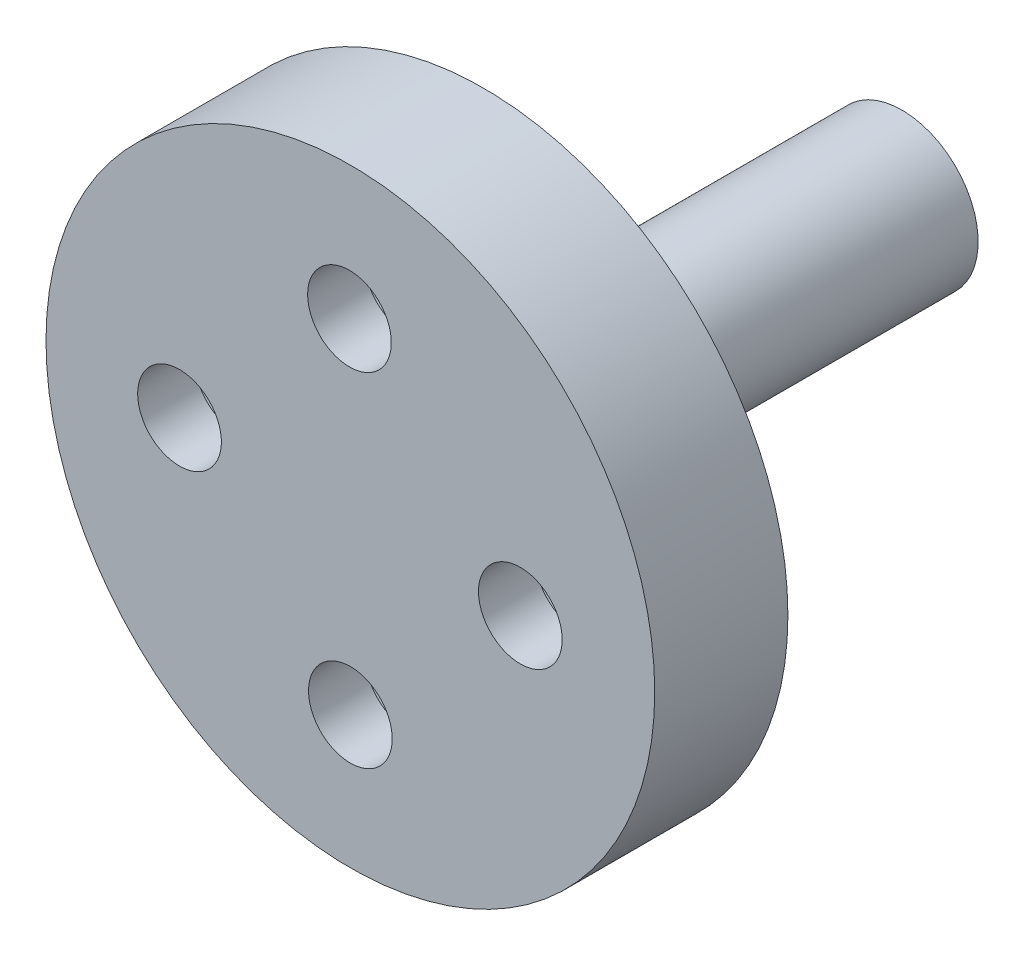
SolidWorks part; units mm, degrees
ref_plane "Front Plane" through (0, 0, 0) normal (0, 0, 1) x (1, 0, 0)
ref_plane "Top Plane" through (0, 0, 0) normal (0, 1, 0) x (1, 0, 0)
ref_plane "Right Plane" through (0, 0, 0) normal (1, 0, 0) x (0, 0, -1)
sketch "Sketch1" plane through (0, 0, 0) normal (0, 1, 0) x (1, 0, 0)
  line L0 (0, 0) -> (8, 0)
  line L1 (8, 0) -> (8, 3.5)
  line L2 (8, 3.5) -> (2, 3.5)
  line L3 (2, 3.5) -> (2, 14.5)
  line L4 (2, 14.5) -> (0, 14.5)
  line L5 (0, 14.5) -> (0, 0)
  dimension "D1" = 8
  dimension "D2" = 14.5
  dimension "D3" = 11
  dimension "D4" = 2
revolve "Revolve1" add sketch "Sketch1" angle 360 about L5
sketch "Sketch2" plane through (0, 0, -3.5) normal (0, 0, -1) x (-1, 0, 0)
  circle A0 centre (0, 0) radius 4.5
  dimension "D1" = 9
hole_wizard "CBORE for M2 SHCS2" positions "Sketch5" profile "Sketch6" counterbore size "M2" standard "ANSI Metric" end condition through all
sketch "Sketch5" plane through (0, 0, -3.5) normal (0, 0, -1) x (-1, 0, 0)
  point P0 (4.4912, 0)
  point P2 (0.0239, 4.4912)
  point P4 (-4.4673, -0.0239)
  point P6 (0, -4.5151)
sketch "Sketch6" plane through (-4.4912, 0, -3.5) normal (1, 0, 0) x (0, 1, 0)
  line L0 (0, 0) -> (0, 3.5)
  line L1 (0, 3.5) -> (1.1, 3.5)
  line L3 (1.1, 3.5) -> (1.1, 2)
  line L4 (1.1, 2) -> (2.2, 2)
  line L5 (2.2, 2) -> (2.2, 0)
  line L7 (2.2, 0) -> (0, 0)
  line L11 (0, -6.35) -> (0, 107.95) construction
  dimension "Thru Hole Dia." = 2.2
  dimension "Thru Hole Depth" = 3.5
  dimension "C'Bore Dia." = 4.4
  dimension "C'Bore Depth" = 2
